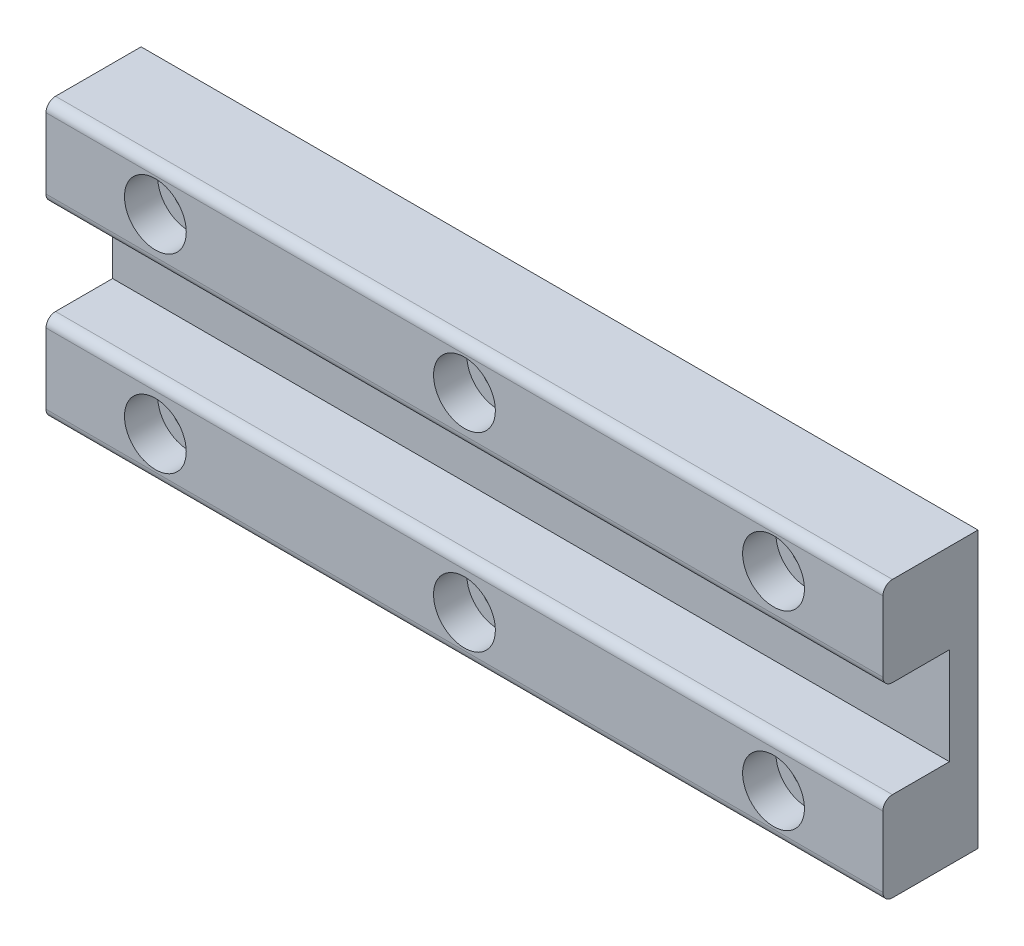
SolidWorks part; units mm, degrees
ref_plane "前视基准面" through (0, 0, 0) normal (0, 0, 1) x (1, 0, 0)
ref_plane "上视基准面" through (0, 0, 0) normal (0, 1, 0) x (1, 0, 0)
ref_plane "右视基准面" through (0, 0, 0) normal (1, 0, 0) x (0, 0, -1)
sketch "草图1" plane through (0, 0, 0) normal (0, 0, 1) x (1, 0, 0)
  line L1 (127.5, -40) -> (-127.5, -40)
  line L2 (127.5, -40) -> (127.5, 40)
  line L3 (127.5, 40) -> (-127.5, 40)
  line L4 (-127.5, -40) -> (-127.5, 40)
  line L5 (127.5, -40) -> (-127.5, 40) construction
  line L6 (127.5, 40) -> (-127.5, -40) construction
  point P0 (0, 0)
  dimension "D1" = 80
  dimension "D2" = 255
extrude "凸台-拉伸1" add sketch "草图1" along normal blind 5
sketch "草图2" plane through (0, 0, 5) normal (0, 0, 1) x (1, 0, 0)
  line L0 (-127.5, 40) -> (-127.5, -40) construction
  circle A0 centre (-107.5, 0) radius 5
  dimension "D1" = 10
  dimension "D2" = 20
extrude "切除-拉伸1" cut sketch "草图2" against normal blind 5
sketch "草图3" plane through (0, 0, 5) normal (0, 0, 1) x (1, 0, 0)
  circle A0 centre (-45, 0) radius 4
  dimension "D2" = 8
extrude "切除-拉伸2" cut sketch "草图3" against normal blind 10
sketch "草图4" plane through (0, 0, 5) normal (0, 0, 1) x (1, 0, 0)
  line L1 (34.5, -10) -> (-53.5, -10)
  line L2 (34.5, -10) -> (34.5, 10)
  line L3 (34.5, 10) -> (-53.5, 10)
  line L4 (-53.5, -10) -> (-53.5, 10)
  line L5 (34.5, -10) -> (-53.5, 10) construction
  line L6 (34.5, 10) -> (-53.5, -10) construction
  line L7 (-127.5, 40) -> (-127.5, -40) construction
  point P0 (-9.5, 0)
  dimension "D1" = 162
  dimension "D2" = 20
  dimension "D3" = 88
extrude "凸台-拉伸2" add sketch "草图4" along normal blind 10
sketch "草图5" plane through (0, 0, 5) normal (0, 0, 1) x (1, 0, 0)
  line L1 (-127.5, 40) -> (-127.5, -40) construction
  circle A0 centre (70, 0) radius 15
  dimension "D1" = 30
  dimension "D2" = 197.5
extrude "切除-拉伸3" cut sketch "草图5" against normal blind 10
sketch "草图6" plane through (0, 0, 0) normal (0, 0, -1) x (-1, 0, 0)
  circle A0 centre (107.5, 0) radius 7
  dimension "D1" = 14
extrude "凸台-拉伸3" add sketch "草图6" against normal blind 15
hole_wizard "M6 螺纹孔1" positions "草图8" profile "草图9" tap size "M6" standard "GB" end condition through all
sketch "草图8" plane through (0, 0, 15) normal (0, 0, 1) x (1, 0, 0)
  point P0 (-107.5, 0)
sketch "草图9" plane through (-107.5, 0, 15) normal (1, 0, 0) x (0, -1, 0)
  line L0 (0, 0) -> (0, 15)
  line L1 (0, 15) -> (2.5, 15)
  line L2 (2.5, 15) -> (2.5, 0)
  line L5 (2.5, 0) -> (0, 0)
  line L11 (0, -6.35) -> (0, 107.95) construction
  dimension "通孔螺纹孔钻头直径" = 5
  dimension "通孔螺纹孔钻头深度" = 15
cosmetic thread "孔螺蚊线1" parameters "D2"=6
sketch "草图10" plane through (0, 0, 15) normal (0, 0, 1) x (1, 0, 0)
  line L0 (-53.5, 0) -> (34.5, 0) construction
  line L1 (-53.5, 10) -> (-53.5, -10) construction
  line L2 (34.5, -10) -> (34.5, 10) construction
  line L3 (-53.5, 5.1) -> (34.5, 5.1)
  line L4 (-53.5, -5.1) -> (34.5, -5.1)
  arc A0 (-53.5, 5.1) -> (-53.5, -5.1) centre (-53.5, 0) ccw
  arc A1 (34.5, -5.1) -> (34.5, 5.1) centre (34.5, 0) ccw
  point P6 (-9.5, 0)
  dimension "D1" = 5.1
extrude "切除-拉伸4" cut sketch "草图10" against normal blind 7
hole_wizard "M4 螺纹孔1" positions "草图11" profile "草图12" tap size "M4" standard "GB" end condition through all
sketch "草图11" plane through (0, 0, 0) normal (0, 0, -1) x (-1, 0, 0)
  point P0 (-39.75, -26.5)
  point P3 (-39.75, -1.5)
  point P6 (-109.9401, -26.5)
  point P8 (-100.25, -1.5)
sketch "草图12" plane through (39.75, -26.5, 0) normal (1, 0, 0) x (0, 1, 0)
  line L0 (0, 0) -> (0, 15)
  line L1 (0, 15) -> (1.65, 15)
  line L2 (1.65, 15) -> (1.65, 0)
  line L5 (1.65, 0) -> (0, 0)
  line L11 (0, -6.35) -> (0, 107.95) construction
  dimension "通孔螺纹孔钻头直径" = 3.3
  dimension "通孔螺纹孔钻头深度" = 15
cosmetic thread "孔螺蚊线2" parameters "D2"=4
cosmetic thread "孔螺蚊线3" parameters "D2"=4
cosmetic thread "孔螺蚊线4" parameters "D2"=4
cosmetic thread "孔螺蚊线5" parameters "D2"=4
fillet "圆角1" radius 10 2 edges at (-127.5, -40, 2.5) (-127.5, 40, 2.5)
sketch "草图13" plane through (0, 0, 5) normal (0, 0, 1) x (1, 0, 0)
  circle A0 centre (-45, 0) radius 6.9694
extrude "凸台-拉伸5" add sketch "草图13" against normal blind 5
sketch "草图14" plane through (0, -40, 0) normal (0, -1, 0) x (1, 0, 0)
  line L1 (127.5, 0) -> (122.5, 0)
  line L2 (127.5, 0) -> (127.5, -75)
  line L3 (127.5, -75) -> (122.5, -75)
  line L4 (122.5, 0) -> (122.5, -75)
  dimension "D1" = 5
  dimension "D2" = 75
extrude "凸台-拉伸6" add sketch "草图14" against normal up to surface (80 mm away) up to face at (5, 40, 2.5)
sketch "草图15" plane through (0, -40, 0) normal (0, -1, 0) x (1, 0, 0)
  line L1 (122.5, -75) -> (102.5, -75)
  line L2 (122.5, -75) -> (122.5, -70)
  line L3 (122.5, -70) -> (102.5, -70)
  line L4 (102.5, -75) -> (102.5, -70)
  dimension "D1" = 5
  dimension "D2" = 20
extrude "凸台-拉伸7" add sketch "草图15" against normal up to surface (80 mm away) up to face at (44.1667, 40, -23.3333)
sketch "草图16" plane through (0, -40, 0) normal (0, -1, 0) x (1, 0, 0)
  line L0 (-32.5, 5) -> (-32.5, 0)
  line L1 (-117.5, 5) -> (127.5, 5) construction
  line L2 (-117.5, 0) -> (122.5, 0) construction
  line L3 (-32.5, 0) -> (102.5, -75)
  line L4 (102.5, -75) -> (127.5, -75)
  line L5 (127.5, -75) -> (127.5, 5)
  line L6 (127.5, 5) -> (-32.5, 5)
  dimension "D1" = 160
extrude "凸台-拉伸8" add sketch "草图16" against normal blind 5
mirror "镜向1" about plane through (0, 0, 0) normal (0, 1, 0) of "凸台-拉伸8"
sketch "草图17" plane through (0, 0, -75) normal (0, 0, -1) x (-1, 0, 0)
  circle A0 centre (-114.5, -15) radius 3
  circle A1 centre (-114.5, 15) radius 3
  dimension "D1" = 6
extrude "切除-拉伸5" cut sketch "草图17" against normal blind 5
fillet "圆角2" radius 1 20 edges at (-124.5711, 37.0711, 5) (-127.5, 0, 5) (-124.5711, -37.0711, 5) (-124.5711, 37.0711, 0) (-127.5, 0, 0) (-124.5711, -37.0711, 0) (5, 40, 5) (-75, 40, 0) (35, 40, -37.5) (115, 40, -75) (127.5, 0, -75) (127.5, 0, 5) (127.5, 40, -35) (5, -40, 5) (127.5, -40, -35) (115, -40, -75) (35, -40, -37.5) (-75, -40, 0) (35, -35, -37.5) (35, 35, -37.5)
fillet "圆角3" [suppressed] radius 1
sketch "草图18" plane through (0, 0, 5) normal (0, 0, 1) x (1, 0, 0)
  line L1 (154.807, -67.1452) -> (-154.807, -67.1452)
  line L2 (154.807, -67.1452) -> (154.807, 67.1452)
  line L3 (154.807, 67.1452) -> (-154.807, 67.1452)
  line L4 (-154.807, -67.1452) -> (-154.807, 67.1452)
  line L5 (154.807, -67.1452) -> (-154.807, 67.1452) construction
  line L6 (154.807, 67.1452) -> (-154.807, -67.1452) construction
  point P0 (0, 0)
extrude "切除-拉伸6" cut sketch "草图18" against normal through all
sketch "草图19" plane through (0, 0, 15) normal (0, 0, 1) x (1, 0, 0)
  circle A2 centre (-107.5, 0) radius 17
  circle A3 centre (-107.5, 0) radius 17
  dimension "D1" = 10
extrude "切除-拉伸7" cut sketch "草图19" against normal through all
sketch "草图20" plane through (34.5, 0, 0) normal (1, 0, 0) x (0, 0, -1)
  line L1 (-15, 10) -> (-5, 10)
  line L2 (-15, 10) -> (-15, 14.5)
  line L3 (-15, 14.5) -> (-5, 14.5)
  line L4 (-5, 10) -> (-5, 14.5)
  dimension "D1" = 4.5
extrude "凸台-拉伸9" add sketch "草图20" against normal up to surface (88 mm away) up to face at (-53.5, 0, 10.75)
mirror "镜向2" about plane through (0, 0, 0) normal (0, 1, 0) of "凸台-拉伸9"
sketch "草图21" plane through (0, 0, 15) normal (0, 0, 1) x (1, 0, 0)
  line L0 (-9.5, 14.5) -> (-9.5, -14.5) construction
  line L1 (-53.5, 14.5) -> (34.5, 14.5) construction
  line L2 (-53.5, -14.5) -> (34.5, -14.5) construction
  line L4 (23, -10) -> (-42, -10) construction
  line L5 (23, -10) -> (23, 10) construction
  line L6 (23, 10) -> (-42, 10) construction
  line L7 (-42, -10) -> (-42, 10) construction
  line L8 (23, -10) -> (-42, 10) construction
  line L9 (23, 10) -> (-42, -10) construction
  circle A0 centre (-42, 10) radius 1.75
  circle A1 centre (-9.5, 10) radius 1.75
  circle A2 centre (23, 10) radius 1.75
  circle A3 centre (23, -10) radius 1.75
  circle A4 centre (-9.5, -10) radius 1.75
  circle A5 centre (-42, -10) radius 1.75
  point P6 (-9.5, 0)
  dimension "D3" = 3.5
  dimension "D1" = 20
  dimension "D2" = 65
extrude "切除-拉伸8" cut sketch "草图21" against normal through all
sketch "草图22" plane through (0, 0, 15) normal (0, 0, 1) x (1, 0, 0)
  circle A0 centre (-42, 10) radius 3.25
  circle A1 centre (-9.5, 10) radius 3.25
  circle A2 centre (23, 10) radius 3.25
  circle A3 centre (23, -10) radius 3.25
  circle A4 centre (-9.5, -10) radius 3.25
  circle A5 centre (-42, -10) radius 3.25
  dimension "D1" = 6.5
extrude "切除-拉伸9" cut sketch "草图22" against normal blind 3.5
fillet "圆角4" radius 1 4 edges at (-9.5, -14.5, 15) (-9.5, -5.1, 15) (-9.5, 5.1, 15) (-9.5, 14.5, 15)
